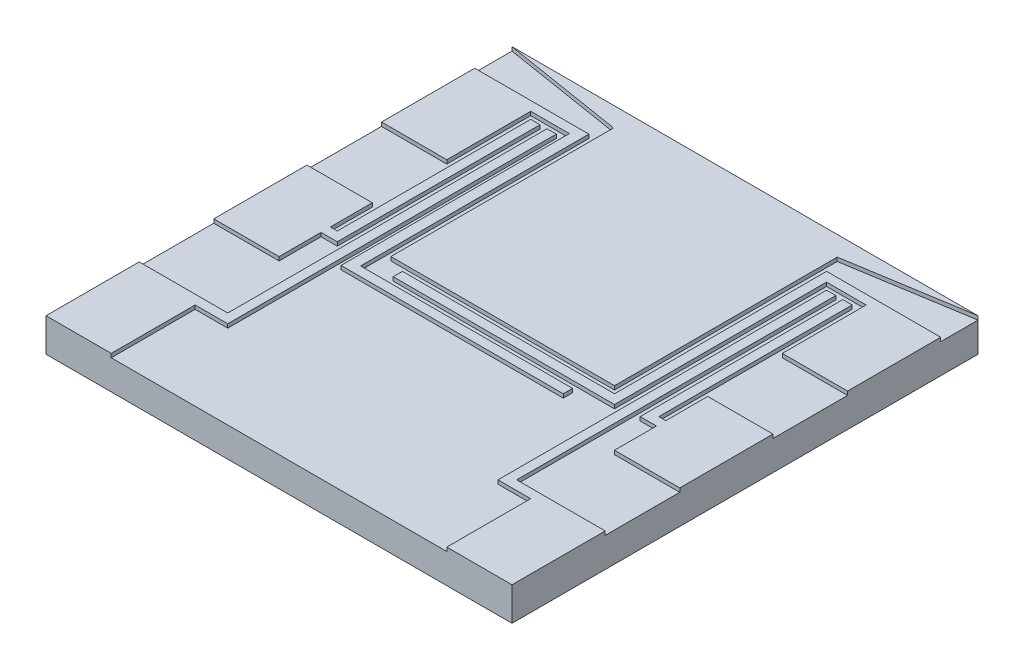
SolidWorks part; units mm, degrees
ref_plane "Front Plane" through (0, 0, 0) normal (0, 0, 1) x (1, 0, 0)
ref_plane "Top Plane" through (0, 0, 0) normal (0, 1, 0) x (1, 0, 0)
ref_plane "Right Plane" through (0, 0, 0) normal (1, 0, 0) x (0, 0, -1)
sketch "Sketch1" plane through (0, 0, 0) normal (0, 1, 0) x (1, 0, 0)
  line L0 (0, 25) -> (6.5, 23.9462)
  line L17 (0, 0) -> (25, 0)
  line L18 (0, 0) -> (0, 25)
  line L39 (0, 25) -> (25, 25)
  line L75 (25, 0) -> (25, 25)
  line L76 (7.5, 23) -> (17.5, 23)
  line L77 (7.5, 23) -> (7.5, 13)
  line L78 (7.5, 13) -> (17.5, 13)
  line L79 (17.5, 23) -> (17.5, 13)
  line L81 (6.5, 23.9462) -> (6.5, 12)
  line L82 (6.5, 12) -> (18.5, 12)
  line L83 (18.5, 23.9462) -> (18.5, 12)
  line L84 (18.5, 23.9462) -> (25, 25)
  line L85 (21.5, 11.75) -> (21.5, 14)
  line L86 (0, 23) -> (3.5035, 23)
  line L88 (0, 18) -> (3.5035, 18)
  line L89 (3.5035, 22.5) -> (3.5035, 18)
  line L90 (0, 14) -> (3.5035, 14)
  line L92 (0, 9) -> (3.5035, 9)
  line L93 (3.5035, 14) -> (3.5035, 11.75)
  line L94 (0, 5) -> (3.5, 5)
  line L100 (25, 5) -> (21.5, 5)
  line L101 (21.5, 0) -> (21.5, 4.5)
  line L102 (25, 9) -> (21.5, 9)
  line L104 (25, 14) -> (21.5, 14)
  line L105 (21.5, 9) -> (21.5, 11.25)
  line L106 (25, 23) -> (21.5, 23)
  line L108 (25, 18) -> (21.5, 18)
  line L109 (21.5, 22.5) -> (21.5, 18)
  line L110 (3.5035, 23) -> (6.125, 23)
  line L112 (3.5035, 22.5) -> (5.5769, 22.5)
  line L115 (6.125, 23) -> (6.125, 10.75)
  line L117 (5.5769, 22.5) -> (5.5769, 10.25)
  line L118 (5.5769, 10.25) -> (17.5, 10.25)
  line L120 (6.125, 10.75) -> (17.5, 10.75)
  line L121 (17.5, 10.25) -> (17.5, 10.75)
  line L122 (21.5, 23) -> (18.875, 23)
  line L124 (21.5, 22.5) -> (19.375, 22.5)
  line L127 (18.875, 23) -> (18.875, 11.625)
  line L129 (19.375, 22.5) -> (19.375, 11.125)
  line L130 (19.375, 11.125) -> (7.5, 11.125)
  line L132 (18.875, 11.625) -> (7.5, 11.625)
  line L133 (7.5, 11.125) -> (7.5, 11.625)
  line L134 (3.5035, 11.75) -> (3.8785, 11.75)
  line L136 (3.5035, 11.25) -> (4.3785, 11.25)
  line L139 (4.3785, 11.25) -> (4.3785, 22.125)
  line L140 (4.3785, 22.125) -> (3.8785, 22.125)
  line L141 (3.8785, 11.75) -> (3.8785, 22.125)
  line L142 (21.5, 11.25) -> (20.625, 11.25)
  line L144 (21.5, 11.75) -> (21.125, 11.75)
  line L147 (20.625, 11.25) -> (20.625, 22.125)
  line L148 (20.625, 22.125) -> (21.125, 22.125)
  line L149 (21.125, 11.75) -> (21.125, 22.125)
  line L150 (3.5035, 11.25) -> (3.5035, 9)
  line L151 (3.5, 4.5) -> (3.5, 0)
  line L152 (3.5, 5) -> (4.75, 5)
  line L154 (3.5, 4.5) -> (5.25, 4.5)
  line L157 (5.25, 4.5) -> (5.25, 22.125)
  line L158 (5.25, 22.125) -> (4.75, 22.125)
  line L159 (4.75, 5) -> (4.75, 22.125)
  line L161 (21.5, 5) -> (20.25, 5)
  line L163 (21.5, 4.5) -> (19.75, 4.5)
  line L166 (19.75, 4.5) -> (19.75, 22.125)
  line L167 (19.75, 22.125) -> (20.25, 22.125)
  line L168 (20.25, 5) -> (20.25, 22.125)
  dimension "D1" = 4.75
extrude "Boss-Extrude2" add sketch "Sketch1" along normal blind 0.2043 contours L159 L152 L94 L18 L17 L151 L154 L157 L158 | L150 L136 L139 L140 L141 L134 L93 L90 L18 L92 | L118 L121 L120 L115 L110 L86 L18 L88 L89 L112 L117 | L83 L84 L39 L0 L81 L82 L76 L79 L78 L77 | L79 L76 L77 L78 | L133 L130 L129 L124 L109 L108 L75 L106 L122 L127 L132 | L144 L149 L148 L147 L142 L105 L102 L75 L104 L85 | L161 L168 L167 L166 L163 L101 L17 L75 L100
sketch "Sketch3" plane through (0, 0, 0) normal (0, 1, 0) x (1, 0, 0)
  line L0 (21.5, 0) -> (25, 0) construction
  line L1 (0, 25) -> (25, 25)
  line L2 (0, 25) -> (0, 0)
  line L3 (0, 0) -> (25, 0)
  line L4 (25, 25) -> (25, 0)
extrude "Boss-Extrude3" add sketch "Sketch3" against normal blind 1.5875
